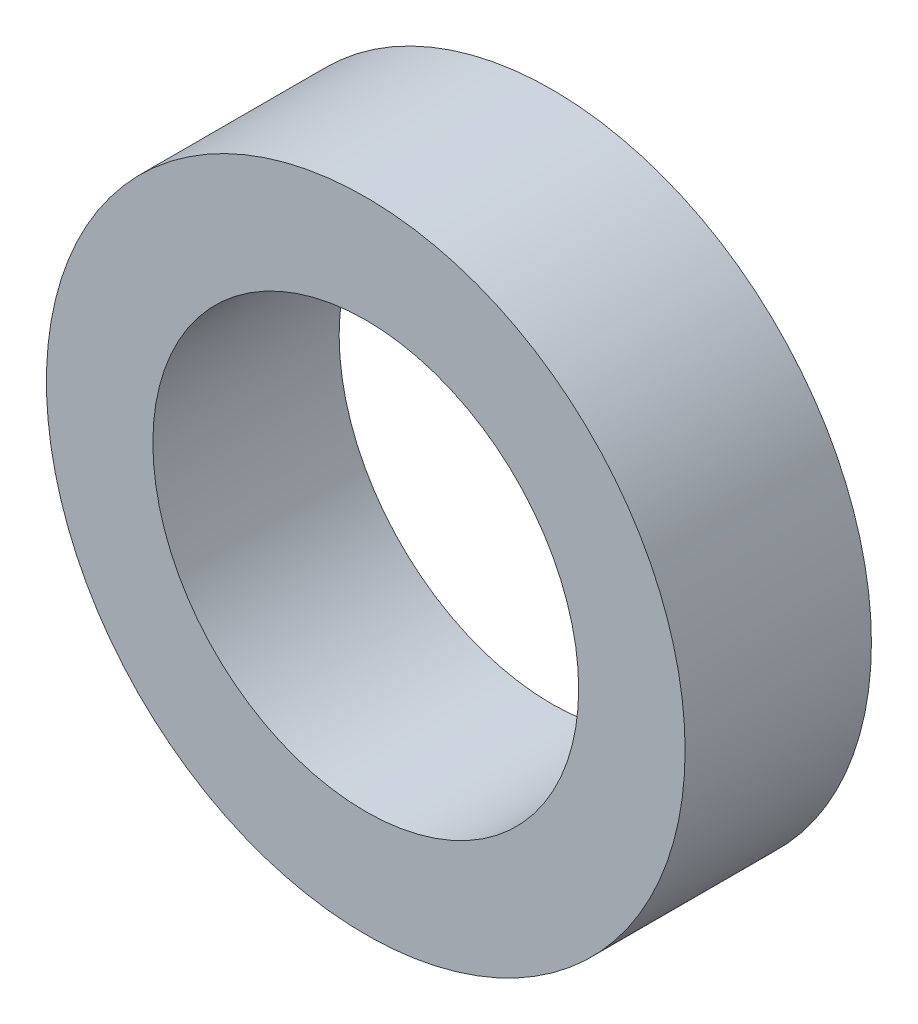
SolidWorks part; units mm, degrees
ref_plane "Front" through (0, 0, 0) normal (0, 0, 1) x (1, 0, 0)
ref_plane "Top" through (0, 0, 0) normal (0, 1, 0) x (1, 0, 0)
ref_plane "Right" through (0, 0, 0) normal (1, 0, 0) x (0, 0, -1)
sketch "Esquisse1" plane through (0, 0, 0) normal (0, 0, 1) x (1, 0, 0)
  circle A0 centre (0, 0) radius 4
  circle A1 centre (0, 0) radius 6
  dimension "D1" = 8
  dimension "D2" = 12
extrude "Boss.-Extru.1" add sketch "Esquisse1" along normal blind 3.5
